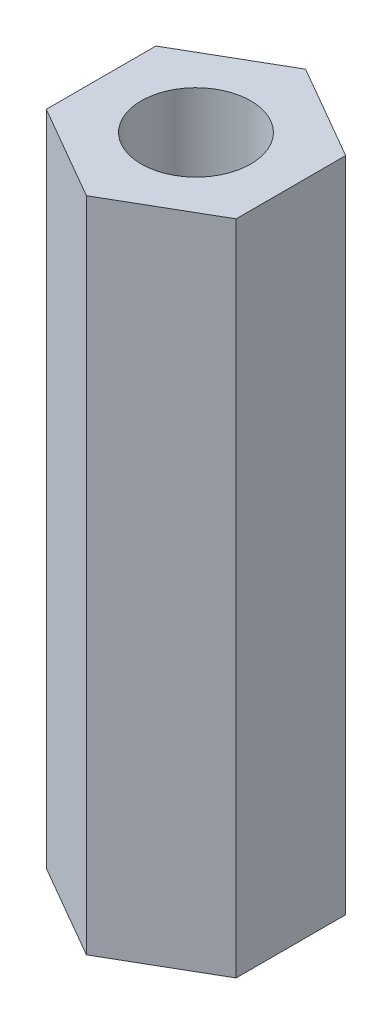
SolidWorks part; units mm, degrees
ref_plane "Face" through (0, 0, 0) normal (0, 0, 1) x (1, 0, 0)
ref_plane "Dessus" through (0, 0, 0) normal (0, 1, 0) x (1, 0, 0)
ref_plane "Droite" through (0, 0, 0) normal (1, 0, 0) x (0, 0, -1)
sketch "Esquisse1" plane through (0, 0, 0) normal (0, 1, 0) x (1, 0, 0)
  line L0 (0, 0) -> (0, 5.5688) construction
  line L1 (0, 5) -> (-4.3301, 2.5)
  line L2 (-4.3301, 2.5) -> (-4.3301, -2.5)
  line L3 (-4.3301, -2.5) -> (0, -5)
  line L4 (0, -5) -> (4.3301, -2.5)
  line L5 (4.3301, -2.5) -> (4.3301, 2.5)
  line L6 (4.3301, 2.5) -> (0, 5)
  circle A0 centre (0, 0) radius 4.3301 construction
  circle A1 centre (0, 0) radius 2.5
  dimension "D1" = 10
  dimension "D2" = 5
extrude "Extrusion1" add sketch "Esquisse1" along normal blind 30
